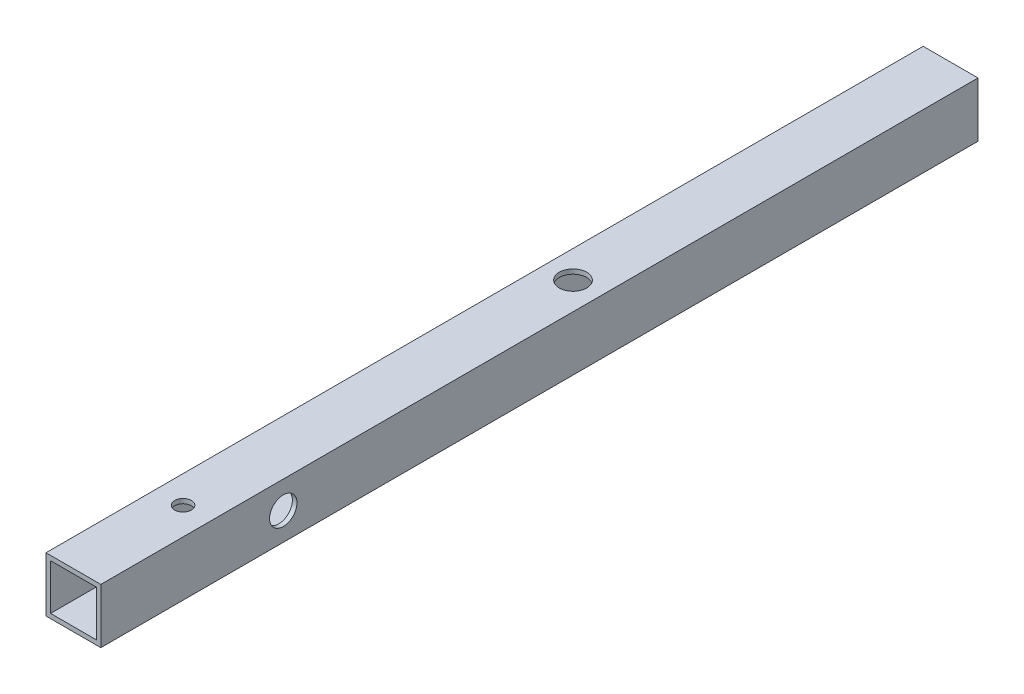
SolidWorks part; units mm, degrees
ref_plane "Front Plane" through (0, 0, 0) normal (0, 0, 1) x (1, 0, 0)
ref_plane "Top Plane" through (0, 0, 0) normal (0, 1, 0) x (1, 0, 0)
ref_plane "Right Plane" through (0, 0, 0) normal (1, 0, 0) x (0, 0, -1)
sketch "Sketch1" plane through (0, 0, 0) normal (0, 0, 1) x (0, -1, 0)
  line L1 (-9.525, 9.525) -> (9.525, 9.525)
  line L2 (-9.525, 9.525) -> (-9.525, -9.525)
  line L3 (-9.525, -9.525) -> (9.525, -9.525)
  line L4 (9.525, 9.525) -> (9.525, -9.525)
  line L5 (-9.525, 9.525) -> (9.525, -9.525) construction
  line L6 (-9.525, -9.525) -> (9.525, 9.525) construction
  line L7 (-7.9375, 7.9375) -> (7.9375, 7.9375)
  line L8 (-7.9375, 7.9375) -> (-7.9375, -7.9375)
  line L9 (-7.9375, -7.9375) -> (7.9375, -7.9375)
  line L10 (7.9375, 7.9375) -> (7.9375, -7.9375)
  line L11 (-7.9375, 7.9375) -> (7.9375, -7.9375) construction
  line L12 (-7.9375, -7.9375) -> (7.9375, 7.9375) construction
  point P0 (0, 0)
  point P5 (0, 0)
  dimension "D1" = 15.875
  dimension "D2" = 19.05
extrude "Boss-Extrude1" add sketch "Sketch1" along normal mid plane 304.8
sketch "Sketch2" plane through (0, 9.525, 0) normal (0, 1, 0) x (1, 0, 0)
  line L0 (0, -152.4) -> (0, -114.3) construction
  line L1 (9.525, -152.4) -> (-9.525, -152.4) construction
  circle A0 centre (0, -114.3) radius 2.8956
  dimension "D1" = 5.7912
  dimension "D2" = 38.1
extrude "Baseplate Mount Hole" cut sketch "Sketch2" against normal through all
sketch "Sketch3" plane through (-9.525, 0, 0) normal (-1, 0, 0) x (0, 0, 1)
  line L0 (-44.45, 0) -> (0, 0) construction
  line L1 (152.4, 9.525) -> (152.4, -9.525) construction
  circle A0 centre (-44.45, 0) radius 4.7625
  dimension "D1" = 196.85
  dimension "D2" = 9.525
extrude "PS Bracket Mount Hole" cut sketch "Sketch3" against normal up to next
sketch "Sketch4" plane through (0, 9.525, 0) normal (0, 1, 0) x (1, 0, 0)
  line L0 (9.525, -152.4) -> (-9.525, -152.4) construction
  circle A1 centre (0, 21.2005) radius 4.7625
  dimension "D1" = 9.525
  dimension "D2" = 173.6005
extrude "Cut-Extrude1" cut sketch "Sketch4" against normal up to next
sketch "Sketch5" plane through (9.525, 0, 0) normal (1, 0, 0) x (0, 0, -1)
  line L0 (-152.4, -9.525) -> (-152.4, 9.525) construction
  circle A0 centre (-89.0016, 0) radius 4.7625
  dimension "D1" = 9.525
  dimension "D2" = 63.3984
extrude "Cut-Extrude2" cut sketch "Sketch5" against normal up to next contours A0
equation "\"Height\"= 32in"
equation "\"Width\"= 23in"
equation "\"Depth\"= 20in"
equation "\"Plexi\"= .121in"
equation "\"MagnetThickness\"= 0.125in"
equation "\"MagnetDiameter\"= 12mm"
equation "\"DoorPlexi\" = \"Plexi\""
equation "\"BasePlateThickness\" = 0.5in"
equation "\"BasePlateWidth\" = \"Width\"+\"EBWidth\"-2*\"Plexi\""
equation "\"BasePlateDepth\" = \"TopBarDepth\"+2*\"CornerCube\""
equation "\"Boxsize\" = .75in"
equation "\"Boxinner\" = .625in"
equation "\"CornerCube\" = 0.75in"
equation "\"FingerLength\" = 1.125in"
equation "\"FingerWidth\" = .625in"
equation "\"Cutwidth\"= .016in"
equation "\"Earsize\"= 1in + \"Cutwidth\" /2"
equation "\"Slotsize\" = 1in - \"CutWidth\" / 2"
equation "\"InnerWidth\" = \"Width\" - 2* \"Plexi\""
equation "\"InnerHeight\" = \"Height\" -2 * \"Plexi\""
equation "\"InnerDepth\" = \"Depth\" - 2*\"Plexi\""
equation "\"RearNumHoles\" = 4"
equation "\"RearHolesBorder\" = 2.25"
equation "\"RearHoleSpacing\" = (\"Width\" - 2*\"RearHolesBorder\") / (\"RearNumHoles\"-1)"
equation "\"RearBarLength\" = (\"InnerWidth\"-2*\"CornerCube\")"
equation "\"RearTopNumHoles\" = 4"
equation "\"RearTopHolesBorder\" = 3.1"
equation "\"RearTopHolesSpacing\" = (\"Width\" - 2*\"RearTopHolesBorder\") / (\"RearTopNumHoles\"-1)"
equation "\"SideTopNumHoles\" = 4"
equation "\"SideTopHoleOffset\"=\"CornerCube\"+\"FingerLength\"+\"Plexi\"+.5"
equation "\"SideHorizNumHoles\" = 4"
equation "\"SideHorizHoleBorder\" = 1.50"
equation "\"SideVertBarLength\"=\"Height\"-\"BasePlateThickness\"-2*\"CornerCube\"-\"Plexi\""
equation "\"SideVertNumHoles\" = 4"
equation "\"SideVertHolesBorder\" = \"CornerCube\"+\"FingerLength\"+1.50"
equation "\"SideVertHoleSpacing\" = (\"InnerHeight\" - 2*\"SideVertHolesBorder\") / (\"SideVertNumHoles\"-1)"
equation "\"RearSideVertNumHoles\" = 4"
equation "\"RearSideVertHolesBorder\" = 2.4"
equation "\"RearSideVertHoleSpacing\" = (\"InnerHeight\" - 2*\"RearSideVertHolesBorder\") / (\"RearSideVertNumHoles\"-1)"
equation "\"RivetDia\" = .228in"
equation "\"SlotDepth\" = \"Plexi\" + 0.75in + .005in"
equation "\"SideSlotWidth\"   = \"Plexi\"+.005in"
equation "\"SidePanelVertSpacing\" = (\"Height\"-2*(1.75-\"Plexi\")) / 5"
equation "\"BottomPanelSideHoleSpacing\" = (\"InnerDepth\"-2*(1.75-\"Plexi\")) / 4"
equation "\"FrontDoorGap\" = .1in"
equation "\"TopDepth\" = \"Depth\"-\"DoorPlexi\"-\"FrontDoorGap\""
equation "\"TopBarDepth\" = \"Depth\"-\"DoorPlexi\"-\"Plexi\"-2*\"MagnetThickness\"-2*\"CornerCube\""
equation "\"CoolerDepth\" = 12in"
equation "\"D1@Boss-Extrude1\"=\"CoolerDepth\""
equation "\"EBWidth\" = 9in"
equation "\"ComponentMountDia\"=0.1770"
equation "\"ShelfThickness\" = .1250in"
equation "\"BoxsizeHalf\" = \"Boxsize\"/2"
equation "\"SideTopHoleSpacing\" = (\"TopBarDepth\"-2*\"SideTopHoleOffset\") / (\"SideTopNumHoles\"-1)"
equation "\"SideHorizHoleSpacing\" = (\"TopBarDepth\"-2*\"SideHorizHoleBorder\") / (\"SideHorizNumHoles\"-1)"
equation "\"BinderPostDia\" = .228in"
equation "\"ShelfGap\" = 0.5in"
equation "\"ShelfDepth\" = \"TopBarDepth\"+\"CornerCube\"-\"CoolerDepth\""
equation "\"ShelfBarDepth\"=\"ShelfDepth\"-2*\"CornerCube\""
equation "\"ShelfWidth\" = \"EBWidth\"-\"ShelfGap\""
equation "\"ShelfBarWidth\" = \"EBWidth\"-\"Boxsize\""
equation "\"ShelfBarWidthShort\" = \"ShelfBarWidth\"-\"Boxsize\"-\"ShelfGap\""
equation "\"ShelfHeight1\" = 13in"
equation "\"ShelfHeight2\" = 24in"
equation "\"IntakeWidth\"=4in"
equation "\"IntakeHeight\"=2in"
equation "\"ExhaustWidth\"=4in"
equation "\"ExhaustHeight\"=2in"
equation "\"VentSpacing\"=7in"
equation "\"VentVertLocation\"=12.75in"
equation "\"AngleBracketLength\"=20mm"
equation "\"AngleBracketWidth\"=.5in"
equation "\"AngleBracketThickness\"=.125in"
equation "\"AngleBracketHolePos\"=15mm"
equation "\"AngleBracketHoleDia\"=\"Rivet3_16Dia\""
equation "\"ShelfBarAngleHole\"=\"ShelfGap\"+\"Boxsize\"+\"AngleBracketHolePosShort\""
equation "\"PSBracketThickness\" = .0641in"
equation "\"EBForwardMountOffset\" = 4.0in"
equation "\"EBForwardMount\" = 2*\"Boxsize\"+\"CoolerDepth\"+\"EBForwardMountOffset\""
equation "\"D1@Sketch2\"=\"BinderPostDia\""
equation "\"EBRearwardMountOffset\" = 1.5in"
equation "\"EBRearwardMount\"= \"Boxsize\"+\"EBRearwardMountOffset\""
equation "\"D2@Sketch2\"=\"EBRearwardMountOffset\""
equation "\"Rivet3_16Dia\" = .191in"
equation "\"D2@Sketch4\"=\"SideTopHoleOffset\"+\"SideTopHoleSpacing\""
equation "\"AngleBracketLengthShort\"=.625in"
equation "\"AngleBracketLengthLong\"=1in"
equation "\"AngleBracketHolePosShort\"=.358in"
equation "\"AngleBracketHolePosLong\"=.7in"
equation "\"MagSealWidth\" = \"InnerWidth\""
equation "\"MagSealHeight\" = \"Height\"-\"BasePlateThickness\"-\"Plexi\""
equation "\"MagWidth\" = .500in"
equation "\"SiliconeSealOD\" = .3125in"
equation "\"SiliconeSealID\" = .1875in"
equation "\"SiliconeSealWidth\" = \"MagSealWidth\" - 2*\"MagWidth\"-\"SiliconeSealOD\""
equation "\"SiliconeSealHeigth\" = \"MagSealHeight\" - 2*\"MagWidth\"-\"SiliconeSealOD\""
equation "\"HooknLoopThick\" = .085in"
equation "\"HooknLoopWidth\" = 0.75in"
equation "\"HooknLoopHeigth\" = 0.75in"
equation "\"RivNutHeight\" = 0.015in"
equation "\"D2@Sketch5\"=\"SideTopHoleOffset\""
